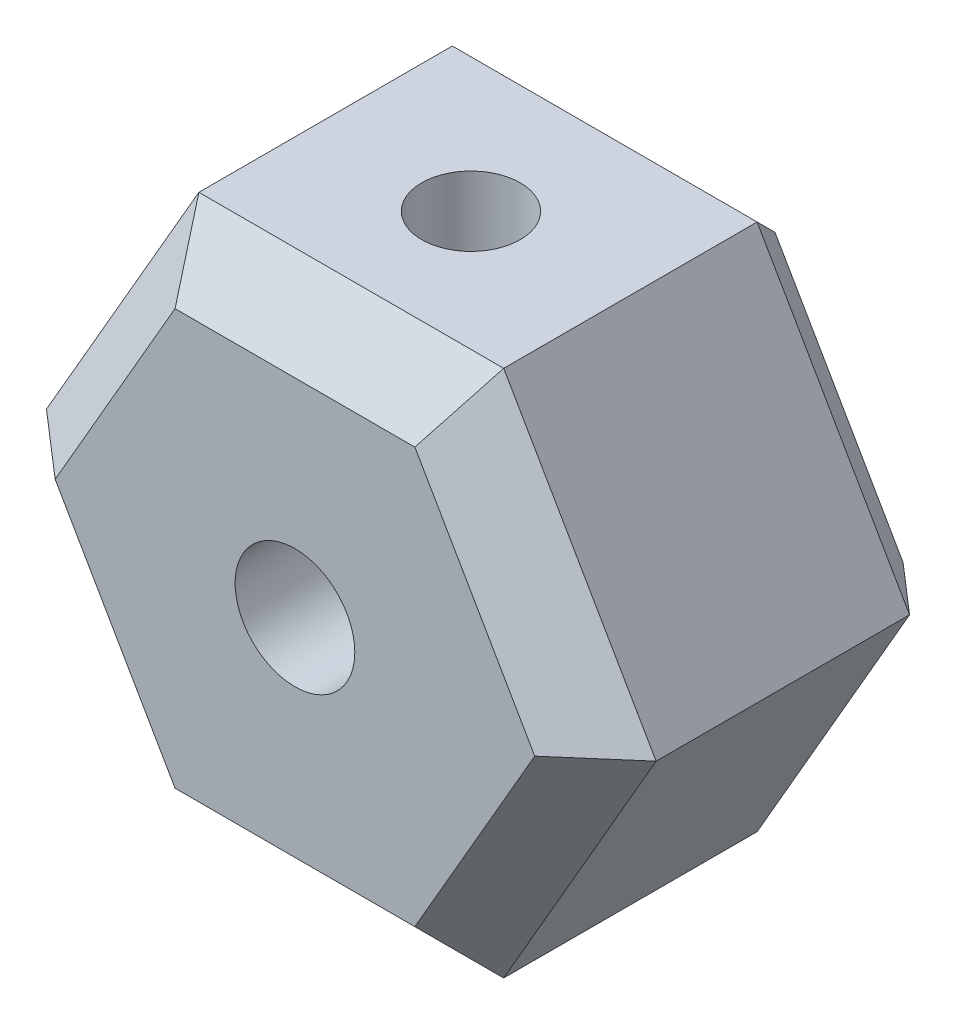
SolidWorks part; units mm, degrees
ref_plane "Front Plane" through (0, 0, 0) normal (0, 0, 1) x (1, 0, 0)
ref_plane "Top Plane" through (0, 0, 0) normal (0, 1, 0) x (1, 0, 0)
ref_plane "Right Plane" through (0, 0, 0) normal (1, 0, 0) x (0, 0, -1)
sketch "Sketch1" plane through (0, 0, 0) normal (0, 0, 1) x (1, 0, 0)
  line L1 (8.6603, 0) -> (4.3301, 7.5)
  line L2 (4.3301, 7.5) -> (-4.3301, 7.5)
  line L3 (-4.3301, 7.5) -> (-8.6603, 0)
  line L4 (-8.6603, 0) -> (-4.3301, -7.5)
  line L5 (-4.3301, -7.5) -> (4.3301, -7.5)
  line L6 (4.3301, -7.5) -> (8.6603, 0)
  circle A0 centre (0, 0) radius 7.5 construction
  circle A1 centre (0, 0) radius 1.7
  dimension "D1" = 3.4
  dimension "D2" = 15
extrude "Boss-Extrude1" add sketch "Sketch1" along normal blind 10
sketch "Sketch2" plane through (0, -7.5, 0) normal (0, -1, 0) x (1, 0, 0)
  line L0 (-4.3301, 5) -> (4.3301, 5) construction
  line L1 (-4.3301, 10) -> (-4.3301, 0) construction
  line L2 (4.3301, 10) -> (4.3301, 0) construction
  circle A0 centre (0, 5) radius 1.4
  dimension "D1" = 2.8
extrude "Cut-Extrude1" cut sketch "Sketch2" against normal through all
chamfer "Chamfer1" distance 1.6 angle 45 6 edges at (-6.4952, -3.75, 10) (0, -7.5, 10) (6.4952, -3.75, 10) (6.4952, 3.75, 10) (0, 7.5, 10) (-6.4952, 3.75, 10)
chamfer "Chamfer2" distance 1.2 angle 45 6 edges at (0, 7.5, 0) (6.4952, 3.75, 0) (6.4952, -3.75, 0) (0, -7.5, 0) (-6.4952, -3.75, 0) (-6.4952, 3.75, 0)
